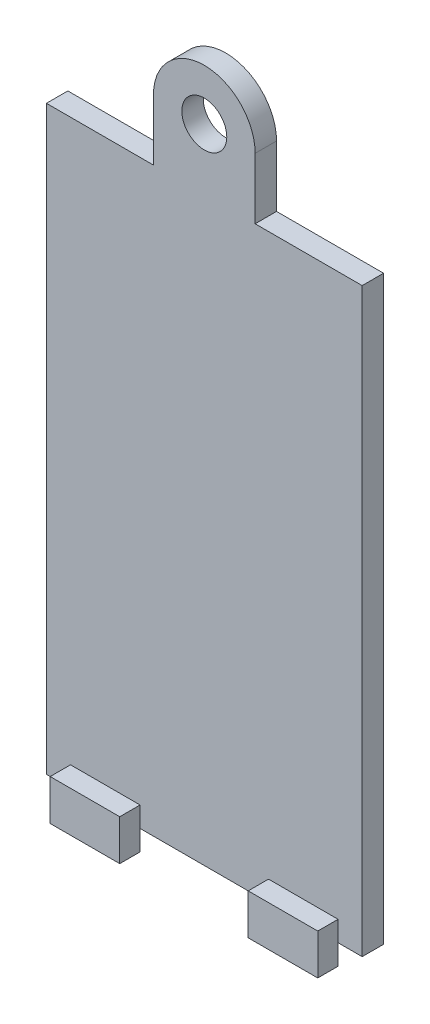
SolidWorks part; units mm, degrees
ref_plane "Front Plane" through (0, 0, 0) normal (1, 0, 0) x (0, 1, 0)
ref_plane "Top Plane" through (0, 0, 0) normal (0, 0, 1) x (0, 1, 0)
ref_plane "Right Plane" through (0, 0, 0) normal (0, 1, 0) x (-1, 0, 0)
sketch "Sketch1" plane through (0, 0, 0) normal (0, 0, 1) x (0, 1, 0)
  line L1 (-27.25, -14.75) -> (27.25, -14.75)
  line L2 (-27.25, -14.75) -> (-27.25, 14.75)
  line L3 (-27.25, 14.75) -> (27.25, 14.75)
  line L4 (27.25, -14.75) -> (27.25, 14.75)
  dimension "D1" = 54.5
  dimension "D2" = 29.5
  dimension "D3" = 14.75
  dimension "D4" = 27.25
extrude "Boss-Extrude1" add sketch "Sketch1" along normal blind 2
sketch "Sketch2" plane through (0, -27.25, 0) normal (0, -1, 0) x (1, 0, 0)
  line L0 (-14.75, 2) -> (14.75, 2) construction
  line L1 (-12.5, 2) -> (-6, 2)
  line L2 (-12.5, 2) -> (-12.5, 3.9)
  line L3 (-12.5, 3.9) -> (-6, 3.9)
  line L4 (-6, 2) -> (-6, 3.9)
  dimension "D1" = 6.5
  dimension "D2" = 2.25
  dimension "D3" = 1.9
extrude "Boss-Extrude2" add sketch "Sketch2" along normal mid plane 3.8
sketch "Sketch4" plane through (0, -27.25, 0) normal (0, -1, 0) x (1, 0, 0)
  line L0 (-6, 2) -> (14.75, 2) construction
  line L1 (6, 2) -> (12.5, 2)
  line L2 (6, 2) -> (6, 3.9)
  line L3 (6, 3.9) -> (12.5, 3.9)
  line L4 (12.5, 2) -> (12.5, 3.9)
  line L5 (14.75, 2) -> (14.75, 0) construction
  dimension "D1" = 6.5
  dimension "D2" = 1.9
  dimension "D3" = 2.25
extrude "Boss-Extrude3" add sketch "Sketch4" along normal mid plane 3.8
sketch "Sketch5" plane through (0, 0, 2) normal (0, 0, 1) x (1, 0, 0)
  line L0 (14.75, 27.25) -> (-14.75, 27.25) construction
  line L1 (-4.75, 32.75) -> (-4.75, 27.25)
  line L2 (-4.75, 27.25) -> (4.75, 27.25)
  line L3 (4.75, 27.25) -> (4.75, 32.75)
  arc A1 (4.75, 32.75) -> (-4.75, 32.75) centre (0, 32.75) ccw
  circle A2 centre (0, 32.75) radius 2.1
  dimension "D2" = 5.5
extrude "Boss-Extrude4" add sketch "Sketch5" against normal blind 2
sketch "Sketch6" plane through (0, 0, 2) normal (0, 0, 1) x (1, 0, 0)
  line L1 (-4.75, 27.25) -> (-20.6503, 27.25)
  line L2 (-4.75, 27.25) -> (-4.75, 27.05)
  line L3 (-4.75, 27.05) -> (-20.6503, 27.05)
  line L4 (-20.6503, 27.25) -> (-20.6503, 27.05)
  line L5 (4.75, 27.25) -> (18.9659, 27.25)
  line L6 (4.75, 27.25) -> (4.75, 27.05)
  line L7 (4.75, 27.05) -> (18.9659, 27.05)
  line L8 (18.9659, 27.25) -> (18.9659, 27.05)
  dimension "D1" = 0.2
  dimension "D2" = 0.2
extrude "Cut-Extrude1" cut sketch "Sketch6" against normal blind 10
